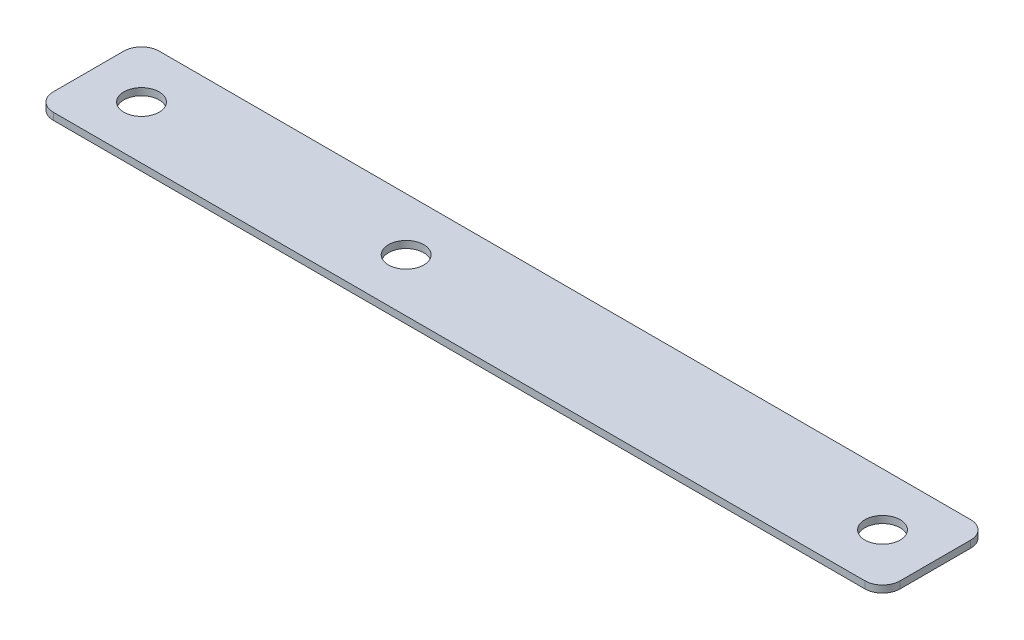
SolidWorks part; units mm, degrees
ref_plane "Front" through (0, 0, 0) normal (0, 0, 1) x (1, 0, 0)
ref_plane "Top" through (0, 0, 0) normal (0, 1, 0) x (1, 0, 0)
ref_plane "Right" through (0, 0, 0) normal (1, 0, 0) x (0, 0, -1)
sketch "Sketch1" plane through (0, 0, 0) normal (0, 1, 0) x (1, 0, 0)
  line L0 (0, 19.05) -> (19.05, 19.05) construction
  line L1 (6.35, 0) -> (298.45, 0)
  line L2 (0, 6.35) -> (0, 31.75)
  line L3 (6.35, 38.1) -> (298.45, 38.1)
  line L4 (304.8, 6.35) -> (304.8, 31.75)
  line L7 (152.4, 38.1) -> (152.4, 0) construction
  line L8 (152.4, 19.05) -> (114.3, 19.05) construction
  circle A0 centre (19.05, 19.05) radius 6.35
  circle A1 centre (285.75, 19.05) radius 6.35
  circle A4 centre (114.3, 19.05) radius 6.35
  arc A5 (298.45, 0) -> (304.8, 6.35) centre (298.45, 6.35) ccw
  arc A6 (298.45, 38.1) -> (304.8, 31.75) centre (298.45, 31.75) cw
  arc A7 (0, 31.75) -> (6.35, 38.1) centre (6.35, 31.75) cw
  arc A8 (6.35, 0) -> (0, 6.35) centre (6.35, 6.35) cw
  point P4 (152.4, 19.05)
  point P18 (304.8, 0)
  point P23 (0, 38.1)
  point P26 (0, 0)
  dimension "D4" = 12.7
  dimension "D5" = 38.1
  dimension "D6" = 12.7
  dimension "D7" = 6.35
  dimension "D1" = 38.1
  dimension "D2" = 304.8
  dimension "D3" = 19.05
extrude "Boss-Extrude1" add sketch "Sketch1" along normal blind 2.54
